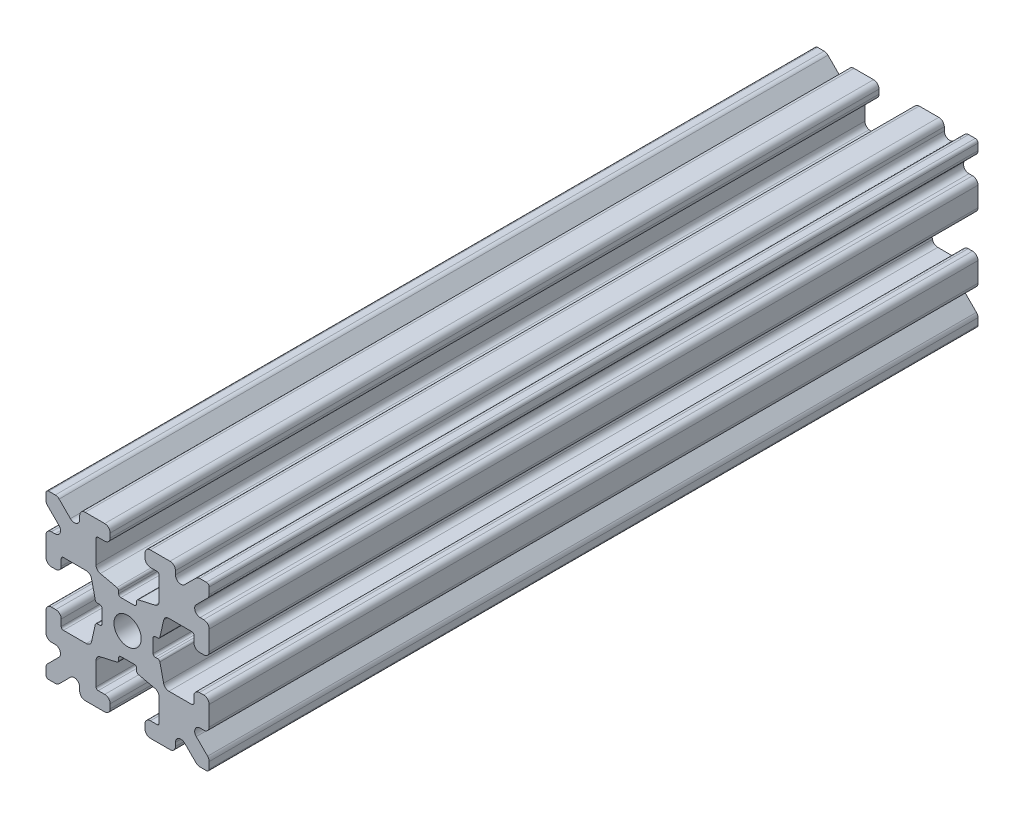
SolidWorks part; units mm, degrees
ref_plane "Front Plane" through (0, 0, 0) normal (0, 0, 1) x (1, 0, 0)
ref_plane "Top Plane" through (0, 0, 0) normal (0, 1, 0) x (1, 0, 0)
ref_plane "Right Plane" through (0, 0, 0) normal (1, 0, 0) x (0, 0, -1)
sketch "Sketch1" plane through (0, 0, 0) normal (0, 0, 1) x (1, 0, 0)
  line L1 (-7.5, -7.5) -> (7.5, -7.5)
  line L2 (-7.5, -7.5) -> (-7.5, 7.5)
  line L3 (-7.5, 7.5) -> (7.5, 7.5)
  line L4 (7.5, -7.5) -> (7.5, 7.5)
  line L5 (-7.5, -7.5) -> (7.5, 7.5) construction
  line L6 (-7.5, 7.5) -> (7.5, -7.5) construction
  circle A0 centre (0, 0) radius 1.25
  point P0 (0, 0)
  dimension "D2" = 2.5
  dimension "D1" = 15
extrude "Boss-Extrude1" add sketch "Sketch1" along normal mid plane 70.678
fillet "Fillet1" radius 0.25 4 edges at (7.5, -7.5, 0) (-7.5, -7.5, 0) (7.5, 7.5, 0) (-7.5, 7.5, 0)
sketch "Sketch2" plane through (0, 0, 35.339) normal (0, 0, 1) x (1, 0, 0)
  line L0 (-7.5, 7.25) -> (-7.5, -7.25) construction
  line L1 (-7.5, 1.6) -> (-6.1, 1.6)
  line L2 (-7.5, 1.6) -> (-7.5, -1.6)
  line L3 (-7.5, -1.6) -> (-6.1, -1.6)
  line L4 (-6.1, 1.6) -> (-6.1, 2.9)
  line L5 (0, 0) -> (-12.1036, 0) construction
  line L6 (-6.1, -2.9) -> (-3.4, -2.9)
  line L7 (0, 0) -> (-7.25, 7.25) construction
  line L8 (-6.1, 2.9) -> (-3.4, 2.9)
  line L9 (-3.4, -2.9) -> (-3.4, 2.9)
  line L10 (55, 0) -> (-55, 0) construction
  line L11 (-6.1, -2.9) -> (-6.1, -1.6)
  line L12 (2.9, 6.1) -> (1.6, 6.1)
  line L13 (2.9, 3.4) -> (-2.9, 3.4)
  line L14 (-2.9, 6.1) -> (-2.9, 3.4)
  line L15 (2.9, 6.1) -> (2.9, 3.4)
  line L16 (-1.6, 6.1) -> (-2.9, 6.1)
  line L17 (1.6, 7.5) -> (1.6, 6.1)
  line L18 (-1.6, 7.5) -> (1.6, 7.5)
  line L19 (-1.6, 7.5) -> (-1.6, 6.1)
  line L20 (-1.6, -7.5) -> (-1.6, -6.1)
  line L21 (-1.6, -7.5) -> (1.6, -7.5)
  line L22 (1.6, -7.5) -> (1.6, -6.1)
  line L23 (-1.6, -6.1) -> (-2.9, -6.1)
  line L24 (2.9, -6.1) -> (2.9, -3.4)
  line L25 (-2.9, -6.1) -> (-2.9, -3.4)
  line L26 (2.9, -3.4) -> (-2.9, -3.4)
  line L27 (2.9, -6.1) -> (1.6, -6.1)
  line L28 (6.1, -2.9) -> (6.1, -1.6)
  line L29 (3.4, -2.9) -> (3.4, 2.9)
  line L30 (6.1, 2.9) -> (3.4, 2.9)
  line L31 (6.1, -2.9) -> (3.4, -2.9)
  line L32 (6.1, 1.6) -> (6.1, 2.9)
  line L33 (7.5, -1.6) -> (6.1, -1.6)
  line L34 (7.5, 1.6) -> (7.5, -1.6)
  line L35 (7.5, 1.6) -> (6.1, 1.6)
  dimension "D1" = 3.2
  dimension "D2" = 5.8
  dimension "D3" = 1.4
  dimension "D4" = 2.7
extrude "Cut-Extrude1" cut sketch "Sketch2" against normal through all
sketch "Sketch4" plane through (0, 0, 35.339) normal (0, 0, 1) x (1, 0, 0)
  line L0 (-3.4, 2.9) -> (-2.75, 0)
  line L1 (55, 0) -> (-55, 0) construction
  line L2 (-2.75, 0) -> (-3.4, -2.9)
  line L3 (-3.4, -2.9) -> (-3.4, 2.9) construction
  line L4 (-3.4, 2.9) -> (-3.4, -2.9)
  line L5 (-2.9, 3.4) -> (0, 2.75)
  line L6 (0, 2.75) -> (2.9, 3.4)
  line L7 (2.9, 3.4) -> (-2.9, 3.4)
  line L8 (3.4, 2.9) -> (2.75, 0)
  line L9 (2.75, 0) -> (3.4, -2.9)
  line L10 (3.4, -2.9) -> (3.4, 2.9)
  line L11 (-2.9, -3.4) -> (0, -2.75)
  line L12 (0, -2.75) -> (2.9, -3.4)
  line L13 (2.9, -3.4) -> (-2.9, -3.4)
  circle A2 centre (0, 0) radius 2.75
  circle A3 centre (0, 0) radius 2.75 construction
  dimension "D1" = 1.5
extrude "Cut-Extrude3" cut sketch "Sketch4" against normal through all
fillet "Fillet3" radius 0.5 16 edges at (-6.1, -1.6, 0) (-7.5, -1.6, 0) (-6.1, 1.6, 0) (-7.5, 1.6, 0) (-1.6, -7.5, 0) (-1.6, -6.1, 0) (1.6, -7.5, 0) (1.6, -6.1, 0) (6.1, -1.6, 0) (7.5, -1.6, 0) (7.5, 1.6, 0) (6.1, 1.6, 0) (1.6, 7.5, 0) (1.6, 6.1, 0) (-1.6, 7.5, 0) (-1.6, 6.1, 0)
fillet "Fillet4" radius 0.5 8 edges at (-3.4, 2.9, 0) (-3.4, -2.9, 0) (2.9, -3.4, 0) (-2.9, -3.4, 0) (3.4, -2.9, 0) (3.4, 2.9, 0) (-2.9, 3.4, 0) (2.9, 3.4, 0)
fillet "Fillet5" radius 3 4 edges at (0, -2.75, 0) (2.75, 0, 0) (-2.75, 0, 0) (0, 2.75, 0)
fillet "Fillet6" radius 0.2 8 edges at (-2.9, -6.1, 0) (2.9, -6.1, 0) (6.1, -2.9, 0) (6.1, 2.9, 0) (2.9, 6.1, 0) (-2.9, 6.1, 0) (-6.1, -2.9, 0) (-6.1, 2.9, 0)
sketch "Sketch5" plane through (0, 0, 35.339) normal (0, 0, 1) x (1, 0, 0)
  line L0 (0, 0) -> (-7.25, 7.25) construction
  line L1 (-7.5, 6.4393) -> (-5.4607, 4.4)
  line L2 (-6.4393, 7.5) -> (-4.4, 5.4607)
  line L3 (-7.5, 4.4) -> (-5.4607, 4.4)
  line L4 (-3.8003, 2.9) -> (-5.9, 2.9) construction
  line L5 (0, 0) -> (-12.1819, 0) construction
  line L6 (-4.4, 7.5) -> (-4.4, 5.4607)
  line L7 (-2.9, 5.9) -> (-2.9, 3.8003) construction
  line L8 (-7.5, 6.4393) -> (-7.5, 4.4)
  line L9 (-7.5, 7.25) -> (-7.5, 2.1) construction
  line L10 (2.1, -7.5) -> (7.25, -7.5) construction
  line L11 (7.5, -7.25) -> (7.5, -2.1) construction
  line L12 (7.25, 7.5) -> (2.1, 7.5) construction
  line L13 (-2.1, 7.5) -> (-7.25, 7.5) construction
  line L14 (-4.4, 7.5) -> (-6.4393, 7.5)
  line L16 (55, 0) -> (-55, 0) construction
  line L17 (0, 0) -> (0, 10.993) construction
  line L18 (0, -54.6431) -> (0, 54.6431) construction
  line L20 (4.4, 7.5) -> (6.4393, 7.5)
  line L22 (7.5, 6.4393) -> (7.5, 4.4)
  line L23 (4.4, 7.5) -> (4.4, 5.4607)
  line L24 (7.5, 4.4) -> (5.4607, 4.4)
  line L25 (6.4393, 7.5) -> (4.4, 5.4607)
  line L26 (7.5, 6.4393) -> (5.4607, 4.4)
  line L27 (7.5, -6.4393) -> (5.4607, -4.4)
  line L28 (6.4393, -7.5) -> (4.4, -5.4607)
  line L29 (7.5, -4.4) -> (5.4607, -4.4)
  line L30 (4.4, -7.5) -> (4.4, -5.4607)
  line L31 (7.5, -6.4393) -> (7.5, -4.4)
  line L33 (4.4, -7.5) -> (6.4393, -7.5)
  line L36 (-4.4, -7.5) -> (-6.4393, -7.5)
  line L38 (-7.5, -6.4393) -> (-7.5, -4.4)
  line L39 (-4.4, -7.5) -> (-4.4, -5.4607)
  line L40 (-7.5, -4.4) -> (-5.4607, -4.4)
  line L41 (-6.4393, -7.5) -> (-4.4, -5.4607)
  line L42 (-7.5, -6.4393) -> (-5.4607, -4.4)
  dimension "D1" = 1.5
  dimension "D2" = 1.5
  dimension "D3" = 1.5
extrude "Cut-Extrude4" cut sketch "Sketch5" against normal through all
fillet "Fillet8" radius 0.5 24 edges at (-5.4607, 4.4, 0) (-7.5, 4.4, 0) (-5.4607, -4.4, 0) (-7.5, -4.4, 0) (-4.4, -7.5, 0) (-4.4, -5.4607, 0) (4.4, -7.5, 0) (4.4, -5.4607, 0) (5.4607, -4.4, 0) (7.5, -4.4, 0) (7.5, 4.4, 0) (5.4607, 4.4, 0) (4.4, 5.4607, 0) (4.4, 7.5, 0) (-4.4, 5.4607, 0) (-4.4, 7.5, 0) (-6.4393, 7.5, 0) (-7.5, 6.4393, 0) (6.4393, 7.5, 0) (7.5, 6.4393, 0) (6.4393, -7.5, 0) (7.5, -6.4393, 0) (-6.4393, -7.5, 0) (-7.5, -6.4393, 0)
sketch "Sketch6" plane through (0, 0, 35.339) normal (0, 0, 1) x (1, 0, 0)
  line L0 (0, 0) -> (0, 11.013) construction
  line L1 (0.6561, 2.8971) -> (2.1235, 2.8971) construction
  line L2 (0, -54.6431) -> (0, 54.6431) construction
  line L3 (0, 0) -> (7.25, 7.25) construction
  line L4 (7.5, 0.8255) -> (7.5, -0.8255)
  line L5 (2.3471, 0.8255) -> (7.5, 0.8255)
  line L6 (0, 0) -> (12.4016, 0) construction
  line L7 (0.8255, -7.5) -> (-0.8255, -7.5)
  line L8 (2.3471, -0.8255) -> (2.3471, 0.8255)
  line L9 (0.8255, -2.3471) -> (0.8255, -7.5)
  line L10 (7.5, -0.8255) -> (2.3471, -0.8255)
  line L11 (-7.5, -0.8255) -> (-2.3471, -0.8255)
  line L12 (-2.3471, -0.8255) -> (-2.3471, 0.8255)
  line L13 (-0.8255, -2.3471) -> (0.8255, -2.3471)
  line L14 (-0.8255, 7.5) -> (-0.8255, 2.3471)
  line L15 (-0.8255, 2.3471) -> (0.8255, 2.3471)
  line L16 (-0.8255, -7.5) -> (-0.8255, -2.3471)
  line L17 (0.8255, 2.3471) -> (0.8255, 7.5)
  line L18 (0.8255, 7.5) -> (-0.8255, 7.5)
  line L19 (3.9, 7.5) -> (2.1, 7.5) construction
  line L20 (-2.3471, 0.8255) -> (-7.5, 0.8255)
  line L21 (-7.5, 0.8255) -> (-7.5, -0.8255)
  point P5 (0, -2.5973)
  point P7 (0, 2.5973)
  dimension "D3" = 0.55
  dimension "D1" = 1.651
extrude "Cut-Extrude5" cut sketch "Sketch6" against normal through all
fillet "Fillet10" radius 0.2 16 edges at (-2.935, 0.8255, 0) (-2.935, -0.8255, 0) (2.935, -0.8255, 0) (2.935, 0.8255, 0) (0.8255, 2.935, 0) (-0.8255, 2.935, 0) (-2.3471, 0.8255, 0) (-2.3471, -0.8255, 0) (0.8255, 2.3471, 0) (-0.8255, 2.3471, 0) (2.3471, 0.8255, 0) (2.3471, -0.8255, 0) (0.8255, -2.935, 0) (0.8255, -2.3471, 0) (-0.8255, -2.3471, 0) (-0.8255, -2.935, 0)
